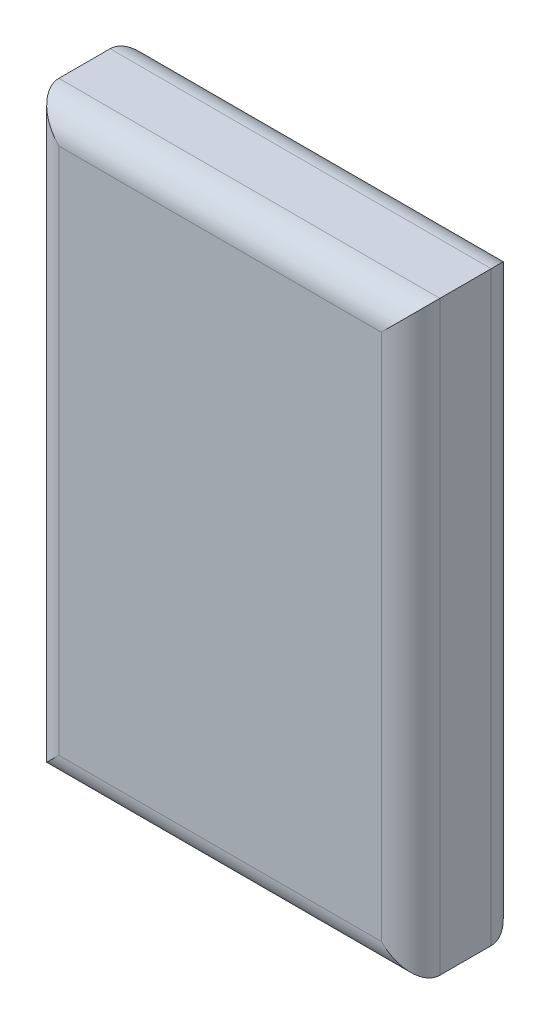
SolidWorks part; units mm, degrees
ref_plane "Front Plane" through (0, 0, 0) normal (0, 0, 1) x (1, 0, 0)
ref_plane "Top Plane" through (0, 0, 0) normal (0, 1, 0) x (1, 0, 0)
ref_plane "Right Plane" through (0, 0, 0) normal (1, 0, 0) x (0, 0, -1)
sketch "Sketch1" plane through (0, 0, 0) normal (0, 0, 1) x (1, 0, 0)
  line L1 (16.51, 25.4) -> (-16.51, 25.4)
  line L2 (16.51, 25.4) -> (16.51, -25.4)
  line L3 (16.51, -25.4) -> (-16.51, -25.4)
  line L4 (-16.51, 25.4) -> (-16.51, -25.4)
  line L5 (16.51, 25.4) -> (-16.51, -25.4) construction
  line L6 (16.51, -25.4) -> (-16.51, 25.4) construction
  point P0 (0, 0)
  dimension "D1" = 50.8
  dimension "D2" = 33.02
extrude "Boss-Extrude1" add sketch "Sketch1" along normal blind 9.525
fillet "Fillet1" radius 2.54 8 edges at (0, -25.4, 0) (16.51, 0, 0) (0, 25.4, 0) (-16.51, 0, 0) (0, 25.4, 9.525) (16.51, 0, 9.525) (0, -25.4, 9.525) (-16.51, 0, 9.525)
